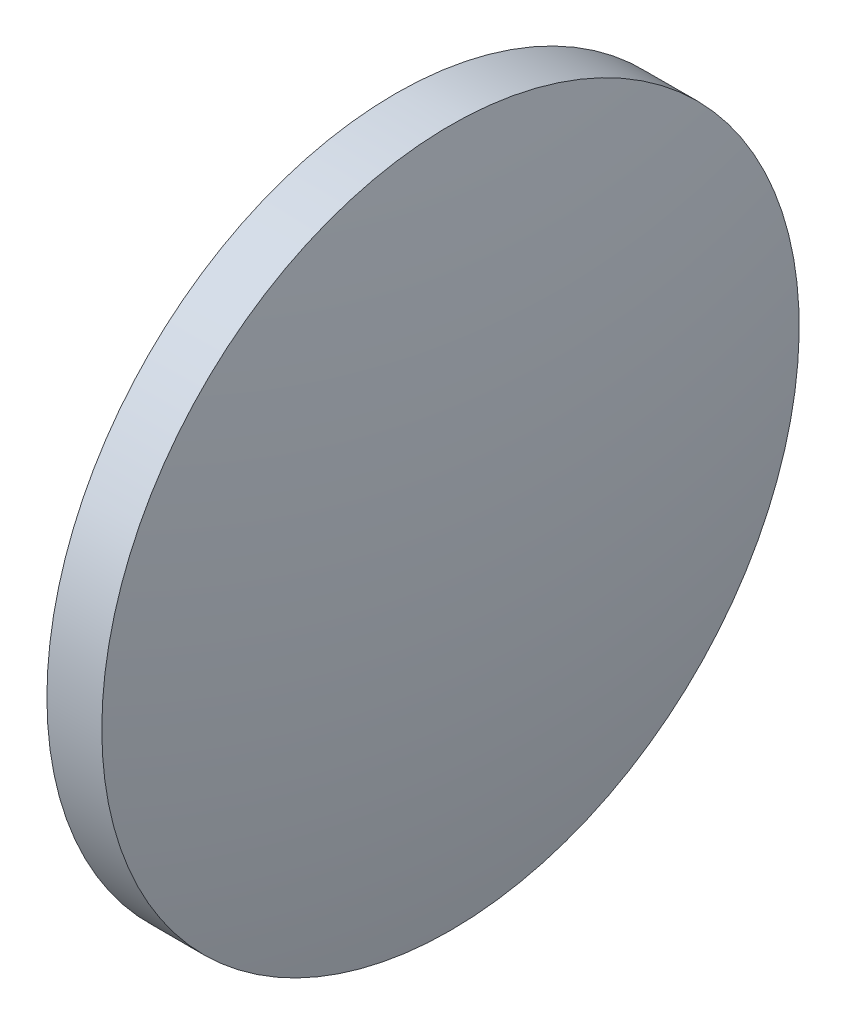
SolidWorks part; units mm, degrees
ref_plane "前视基准面" through (0, 0, 0) normal (0, 0, 1) x (1, 0, 0)
ref_plane "上视基准面" through (0, 0, 0) normal (0, 1, 0) x (1, 0, 0)
ref_plane "右视基准面" through (0, 0, 0) normal (1, 0, 0) x (0, 0, -1)
sketch "草图1" plane through (0, 0, 0) normal (0, 0, 1) x (1, 0, 0)
  line L0 (79.3054, 48.6161) -> (93.4772, 48.6161) construction
  line L1 (85.4585, 61.3161) -> (87.4579, 61.3161)
  line L2 (87.4579, 61.3161) -> (87.4579, 35.9161)
  line L3 (87.4579, 35.9161) -> (85.4585, 35.9161)
  line L4 (85.4585, 35.9161) -> (85.4585, 61.3161)
  arc A0 (85.4585, 61.3161) -> (85.4585, 35.9161) centre (149.3473, 48.6161) ccw
  arc A1 (87.4579, 35.9161) -> (87.4579, 61.3161) centre (23.5691, 48.6161) ccw
  dimension "D1" = 25.4
  dimension "D2" = 1.9993
revolve "旋转1" add sketch "草图1" angle 360 about L0
